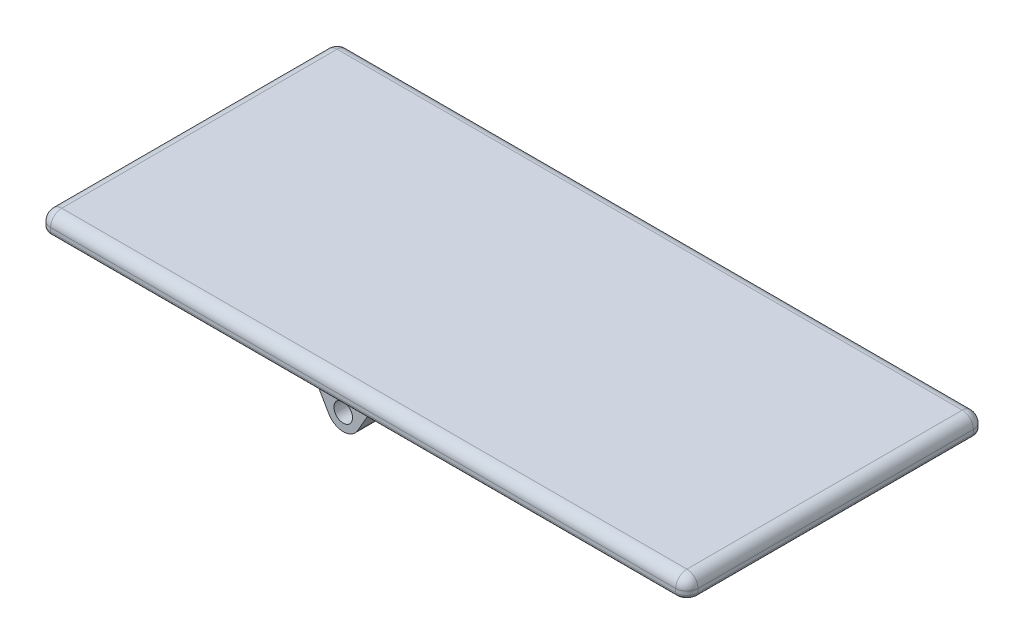
SolidWorks part; units mm, degrees
ref_plane "Front Plane" through (0, 0, 0) normal (0, 0, 1) x (1, 0, 0)
ref_plane "Top Plane" through (0, 0, 0) normal (0, 1, 0) x (1, 0, 0)
ref_plane "Right Plane" through (0, 0, 0) normal (1, 0, 0) x (0, 0, -1)
sketch "Sketch3" plane through (0, 0, 0) normal (0, 0, 1) x (1, 0, 0)
  line L0 (97.6547, 0) -> (97.6547, 5)
  line L1 (97.6547, 5) -> (-76.3479, 5)
  line L2 (-76.3479, 5) -> (-76.3479, 0)
  line L4 (97.6547, 0) -> (0, 0)
  line L5 (0, 0) -> (-76.3479, 0)
  line L8 (95.1551, -29.7586) -> (1.7509, -1.2612) construction
  line L9 (0.2059, -1.0035) -> (-76.0969, 1.6168) construction
  point P2 (0, 0)
  point P10 (0, 0)
  point P11 (0, 0)
  dimension "D1" = 5
extrude "Boss-Extrude3" add sketch "Sketch3" along normal blind 80 separate body
sketch "Sketch2" plane through (0, 0, 0) normal (0, 0, -1) x (-1, 0, 0)
  line L0 (0, 0) -> (0, -7) construction
  line L2 (-3.8971, -9.25) -> (-9.2376, 0)
  line L3 (-9.2376, 0) -> (9.2376, 0)
  line L4 (9.2376, 0) -> (3.8971, -9.25)
  line L5 (4.5, -7) -> (4.5, 0) construction
  line L11 (76.3479, 0) -> (-97.6547, 0) construction
  circle A0 centre (0, -7) radius 2.5
  circle A1 centre (0, -7) radius 5 construction
  circle A2 centre (0, -7) radius 7 construction
  circle A3 centre (0, -7) radius 4.5 construction
  arc A4 (-3.8971, -9.25) -> (3.8971, -9.25) centre (0, -7) ccw
  point P7 (9.3353, -1.1064)
  point P8 (0, 0)
  point P16 (0, 0)
  point P17 (0, 0)
  point P18 (-12.0467, 0)
  point P19 (0, 0)
  point P20 (0, 0)
  point P23 (0, 0)
  point P24 (0, 0)
  dimension "D1" = 5
  dimension "D2" = 10
  dimension "D3" = 2
  dimension "D4" = 0.5
  dimension "D5" = 30
extrude "Boss-Extrude2" add sketch "Sketch2" against normal blind 5 from offset 5.3 offset against normal yes
pattern_linear "LPattern1" count 3 spacing 32.2 along (0, 0, 1) of "Boss-Extrude2"
fillet "Fillet1" radius 3 8 edges at (97.6547, 5, 40) (10.6534, 5, 0) (-76.3479, 5, 40) (10.6534, 5, 80) (97.6547, 2.5, 80) (-76.3479, 2.5, 80) (-76.3479, 2.5, 0) (97.6547, 2.5, 0)
fillet "Fillet2" radius 1 8 edges at (96.776, 0, 79.1213) (10.6534, 0, 80) (-75.4692, 0, 79.1213) (-76.3479, 0, 40) (-75.4692, 0, 0.8787) (10.6534, 0, 0) (96.776, 0, 0.8787) (97.6547, 0, 40)
